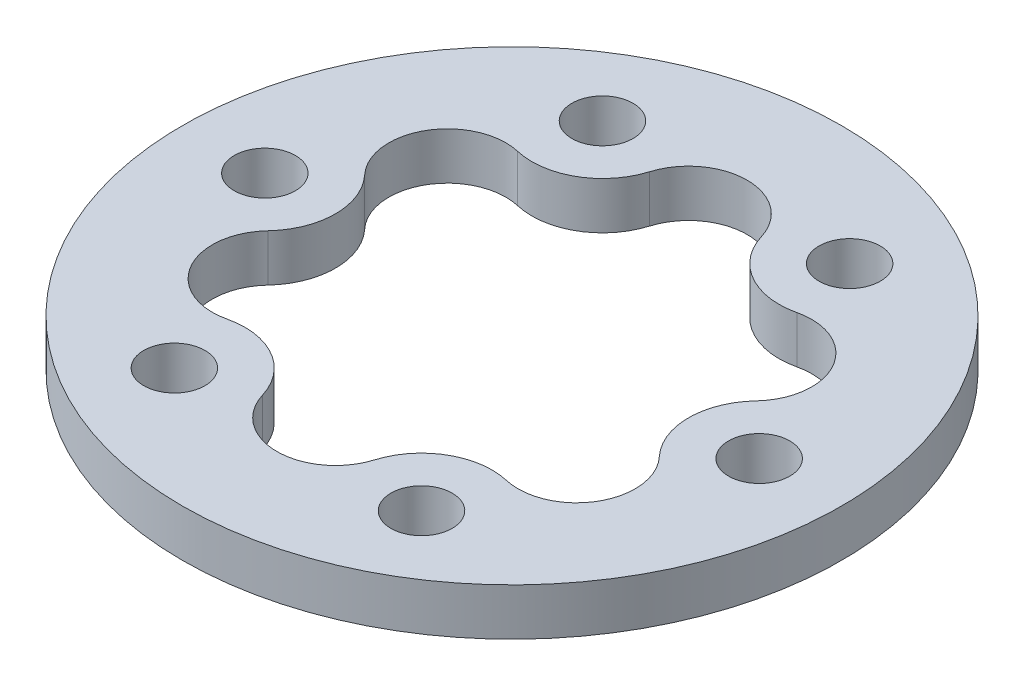
SolidWorks part; units mm, degrees
material "Hexcel AS4C (3000 丝)"
ref_plane "前视基准面" through (0, 0, 0) normal (0, 0, 1) x (1, 0, 0)
ref_plane "上视基准面" through (0, 0, 0) normal (0, 1, 0) x (1, 0, 0)
ref_plane "右视基准面" through (0, 0, 0) normal (1, 0, 0) x (0, 0, -1)
sketch "草图1" plane through (0, 0, 0) normal (0, 1, 0) x (1, 0, 0)
  line L0 (0, 25) -> (0, 0) construction
  line L1 (0, 0) -> (10.5, 18.1865) construction
  circle A0 centre (0, 0) radius 28
  circle A1 centre (0, 0) radius 25 construction
  circle A2 centre (0, 25) radius 1.25 construction
  circle A3 centre (21.6506, 12.5) radius 1.25 construction
  circle A4 centre (21.6506, -12.5) radius 1.25 construction
  circle A5 centre (0, -25) radius 1.25 construction
  circle A6 centre (-21.6506, -12.5) radius 1.25 construction
  circle A7 centre (-21.6506, 12.5) radius 1.25 construction
  circle A8 centre (0, 0) radius 15 construction
  circle A9 centre (0, 15) radius 4 construction
  circle A10 centre (12.9904, -7.5) radius 4 construction
  circle A11 centre (-12.9904, -7.5) radius 4 construction
  circle A12 centre (0, 0) radius 21 construction
  circle A13 centre (10.5, 18.1865) radius 2.6
  circle A14 centre (21, 0) radius 2.6
  circle A15 centre (10.5, -18.1865) radius 2.6
  circle A16 centre (-10.5, -18.1865) radius 2.6
  circle A17 centre (-21, 0) radius 2.6
  circle A18 centre (-10.5, 18.1865) radius 2.6
  dimension "D1" = 2.5
  dimension "D2" = 50
  dimension "D3" = 56
  dimension "D5" = 30
  dimension "D6" = 8
  dimension "D9" = 5.2
  dimension "D10" = 42
  dimension "D8" = 30
  dimension "D4" = 6
  dimension "D7" = 3
  dimension "D11" = 6
extrude "凸台-拉伸1" add sketch "草图1" along normal blind 4
sketch "草图4" plane through (0, 4, 0) normal (0, 1, 0) x (1, 0, 0)
  circle A0 centre (0, 0) radius 15 construction
  circle A1 centre (0, 15) radius 4 construction
  circle A2 centre (12.9904, 7.5) radius 4 construction
  circle A3 centre (12.9904, -7.5) radius 4 construction
  circle A4 centre (0, -15) radius 4 construction
  circle A5 centre (-12.9904, -7.5) radius 4 construction
  circle A6 centre (-12.9904, 7.5) radius 4 construction
  arc A7 (4.7586, 16.4441) -> (11.8617, 12.3431) centre (10.5, 18.1865) ccw
  arc A8 (-4.7586, 16.4441) -> (4.7586, 16.4441) centre (0, 15) cw
  arc A9 (11.8617, 12.3431) -> (16.6203, 4.101) centre (12.9904, 7.5) cw
  arc A10 (16.6203, 4.101) -> (16.6203, -4.101) centre (21, 0) ccw
  arc A11 (16.6203, -4.101) -> (11.8617, -12.3431) centre (12.9904, -7.5) cw
  arc A12 (11.8617, -12.3431) -> (4.7586, -16.4441) centre (10.5, -18.1865) ccw
  arc A13 (4.7586, -16.4441) -> (-4.7586, -16.4441) centre (0, -15) cw
  arc A14 (-4.7586, -16.4441) -> (-11.8617, -12.3431) centre (-10.5, -18.1865) ccw
  arc A15 (-11.8617, -12.3431) -> (-16.6203, -4.101) centre (-12.9904, -7.5) cw
  arc A16 (-16.6203, -4.101) -> (-16.6203, 4.101) centre (-21, 0) ccw
  arc A17 (-16.6203, 4.101) -> (-11.8617, 12.3431) centre (-12.9904, 7.5) cw
  arc A18 (-11.8617, 12.3431) -> (-4.7586, 16.4441) centre (-10.5, 18.1865) ccw
  dimension "D1" = 30
  dimension "D2" = 8
  dimension "D4" = 6
  dimension "D3" = 6
  dimension "D5" = 6
extrude "切除-拉伸2" cut sketch "草图4" against normal through all and the other way through all
move or copy body "实体-移动/复制1" bodies to move or copy 109
